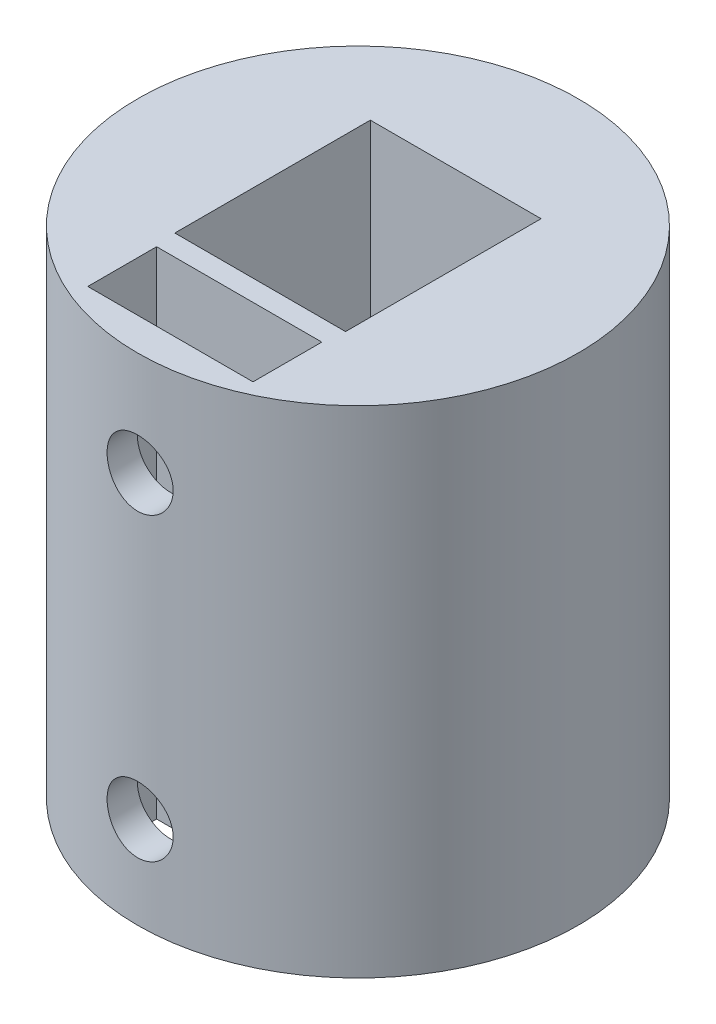
SolidWorks part; units mm, degrees
ref_plane "Front Plane" through (0, 0, 0) normal (0, 0, 1) x (1, 0, 0)
ref_plane "Top Plane" through (0, 0, 0) normal (0, 1, 0) x (1, 0, 0)
ref_plane "Right Plane" through (0, 0, 0) normal (1, 0, 0) x (0, 0, -1)
sketch "Sketch1" plane through (0, 0, 0) normal (0, 1, 0) x (1, 0, 0)
  circle A0 centre (0, 0) radius 8
  dimension "D1" = 16
extrude "Boss-Extrude1" add sketch "Sketch1" along normal blind 18
sketch "Sketch2" plane through (0, 0, 0) normal (0, -1, 0) x (1, 0, 0)
  line L0 (-1.5013, 1.396) -> (1.5013, 1.396)
  arc A0 (-1.5013, 1.396) -> (1.5013, 1.396) centre (0, 0) ccw
  dimension "D1" = 4.1
  dimension "D2" = 1.396
extrude "Cut-Extrude1" cut sketch "Sketch2" against normal blind 8
sketch "Sketch3" plane through (0, 18, 0) normal (0, 1, 0) x (1, 0, 0)
  line L1 (-3.1, 3.55) -> (3.1, 3.55)
  line L2 (-3.1, 3.55) -> (-3.1, -3.55)
  line L3 (-3.1, -3.55) -> (3.1, -3.55)
  line L4 (3.1, 3.55) -> (3.1, -3.55)
  line L5 (-3.1, 3.55) -> (3.1, -3.55) construction
  line L6 (-3.1, -3.55) -> (3.1, 3.55) construction
  point P0 (0, 0)
  dimension "D1" = 6.2
  dimension "D2" = 7.1
extrude "Cut-Extrude2" cut sketch "Sketch3" against normal blind 8
sketch "Sketch4" plane through (0, 18, 0) normal (0, 1, 0) x (1, 0, 0)
  line L0 (-3, -4.3116) -> (3, -4.3116)
  line L1 (3, -4.3116) -> (3, -6.8116)
  line L2 (3, -6.8116) -> (-3, -6.8116)
  line L3 (-3, -6.8116) -> (-3, -4.3116)
  line L4 (0, 8.8759) -> (0, 0) construction
  dimension "D1" = 6
  dimension "D2" = 2.5
extrude "Cut-Extrude3" cut sketch "Sketch4" against normal blind 20 contours L0 L1 L2 L3
ref_plane "Plane1" through (0, 0, 8) normal (0, 0, 1) x (1, 0, 0)
sketch "Sketch5" plane through (0, 0, 8) normal (0, 0, 1) x (1, 0, 0)
  circle A0 centre (0, 3.3283) radius 1.2
  circle A1 centre (0, 14.2258) radius 1.2
  point P0 (0, 14.2258)
  point P1 (0, 3.3283)
  dimension "D1" = 2.4
extrude "Cut-Extrude4" cut sketch "Sketch5" against normal blind 9
